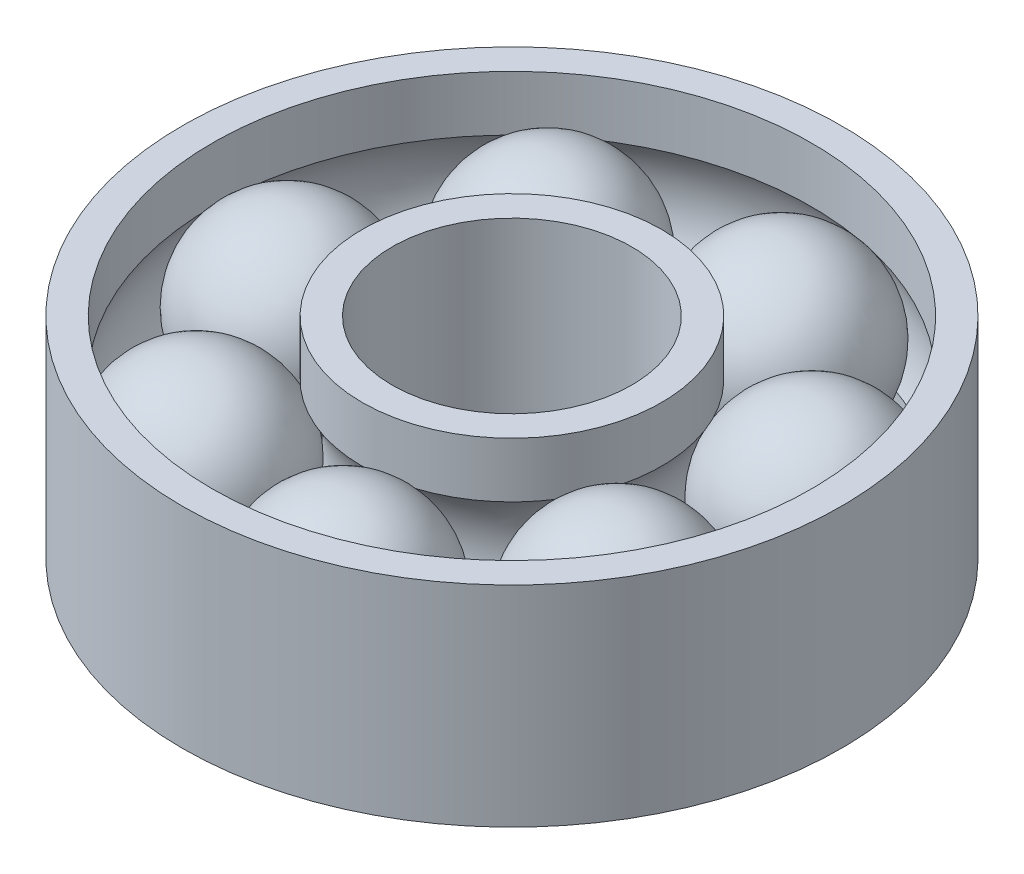
SolidWorks part; units mm, degrees
ref_plane "Front" through (0, 0, 0) normal (0, 0, 1) x (1, 0, 0)
ref_plane "Top" through (0, 0, 0) normal (0, 1, 0) x (1, 0, 0)
ref_plane "Right" through (0, 0, 0) normal (1, 0, 0) x (0, 0, -1)
sketch "Sketch1" plane through (0, 0, 0) normal (0, 0, 1) x (1, 0, 0)
  line L0 (-4, 4.5429) -> (-5, 3.5429) construction
  line L1 (-4, 4.5429) -> (-5, 4.5429)
  line L2 (-4, 4.5429) -> (-4, -2.4571)
  line L3 (-4, -2.4571) -> (-5, -2.4571)
  line L4 (-5, 4.5429) -> (-5, 2.7012)
  line L5 (-4, 4.5429) -> (-5, -2.4571) construction
  line L6 (-4, -2.4571) -> (-5, 4.5429) construction
  line L7 (-10, 4.5429) -> (-11, 4.5429)
  line L8 (-10, 4.5429) -> (-10, 2.7012)
  line L9 (-10, -2.4571) -> (-11, -2.4571)
  line L10 (-11, 4.5429) -> (-11, -2.4571)
  line L11 (-10, 4.5429) -> (-11, -2.4571) construction
  line L12 (-10, -2.4571) -> (-11, 4.5429) construction
  line L14 (-10, -0.6154) -> (-10, -2.4571)
  line L15 (-5, -0.6154) -> (-5, -2.4571)
  arc A0 (-10, 2.7012) -> (-10, -0.6154) centre (-7.5, 1.0429) ccw
  arc A1 (-5, -0.6154) -> (-5, 2.7012) centre (-7.5, 1.0429) ccw
  point P0 (-4.5, 1.0429)
  point P5 (-10.5, 1.0429)
  point P15 (-12.5111, 3.9118)
  dimension "D6" = 6
  dimension "D1" = 1
  dimension "D2" = 7
  dimension "D3" = 11
  dimension "D4" = 4
  dimension "D5" = 0
sketch "Sketch3" plane through (0, 0, 0) normal (0, 0, 1) x (1, 0, 0)
  line L0 (-7.5, 4.0429) -> (-7.5, -1.9571)
  arc A0 (-7.5, 4.0429) -> (-7.5, -1.9571) centre (-7.5, 1.0429) cw
  dimension "D1" = 3
revolve "ball" add sketch "Sketch3" angle 360 about L0
ref_axis "Axis1" through (0, 50, 0) along (0, -1, 0)
revolve "body" add sketch "Sketch1" angle 360 about axis through (0, 50, 0) along (0, -1, 0)
pattern_circular "CirPattern3" count 7 over 360 about axis through (0, 0, 0) along (0, 1, 0) of bodies 101
